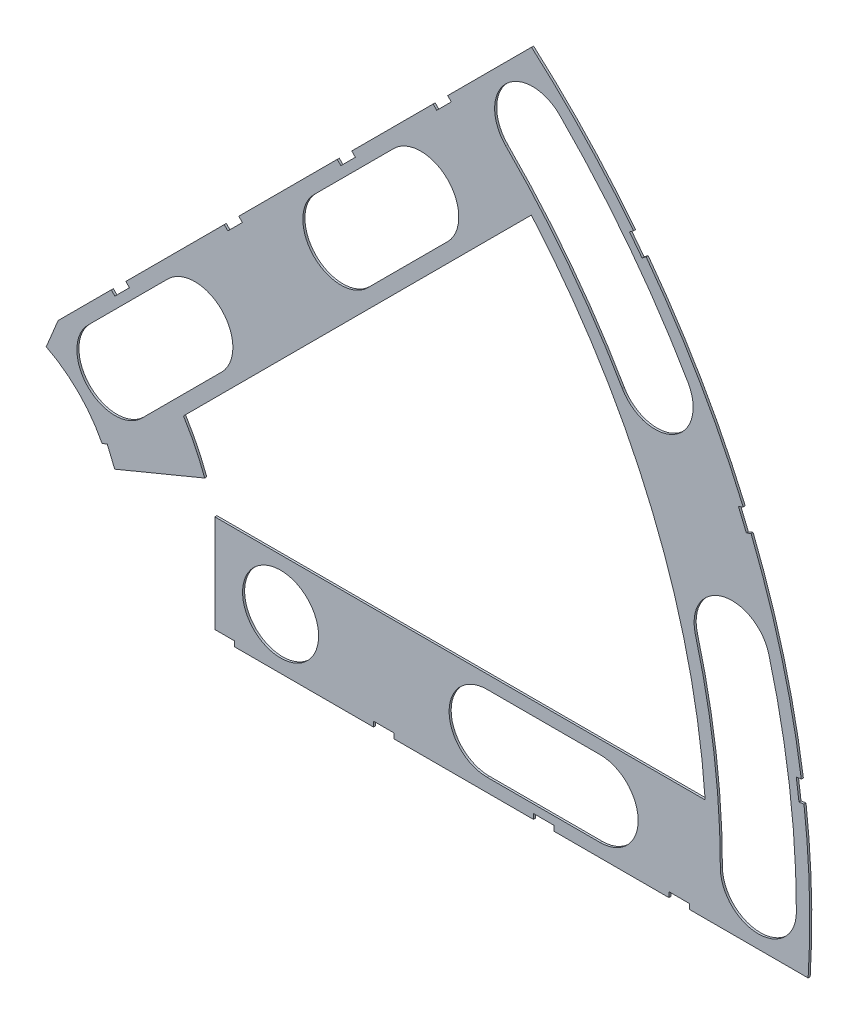
SolidWorks part; units mm, degrees
material "PTFE (general)"
ref_plane "Front Plane" through (0, 0, 0) normal (0, 0, 1) x (1, 0, 0)
ref_plane "Top Plane" through (0, 0, 0) normal (0, 1, 0) x (1, 0, 0)
ref_plane "Right Plane" through (0, 0, 0) normal (1, 0, 0) x (0, 0, -1)
sketch "Sketch1" plane through (0, 0, 0) normal (0, 0, 1) x (1, 0, 0)
  line L0 (0, 0) -> (320.3893, 0) construction
  line L1 (0, 0) -> (155.5285, 155.5285) construction
  line L2 (67.2115, 76.1917) -> (8.6967, 17.6769)
  line L3 (8.6967, 17.6769) -> (7.229, 14.1336)
  line L4 (101.4014, -6.35) -> (18.6489, -6.35)
  line L5 (15.1056, -4.8823) -> (18.6489, -6.35)
  line L6 (88.6729, 6.35) -> (27.8605, 6.35)
  line L9 (67.1914, 58.2111) -> (24.1905, 15.2102)
  line L10 (0, 0) -> (40.4486, 97.6516) construction
  line L11 (0, 0) -> (123.4567, -51.1374) construction
  line L18 (8.6967, 17.6769) -> (13.294, 8.6183) construction
  line L19 (18.6489, -6.35) -> (15.4943, 3.3063) construction
  line L20 (27.8605, 6.35) -> (27.7442, 6.7059) construction
  line L21 (24.1905, 15.2102) -> (24.3599, 14.8764) construction
  arc A0 (7.229, 14.1336) -> (15.1056, -4.8823) centre (0, 0) cw
  arc A1 (67.2115, 76.1917) -> (101.4014, -6.35) centre (0, 0) cw
  arc A2 (24.1905, 15.2102) -> (27.8605, 6.35) centre (0, 0) cw
  arc A3 (67.1914, 58.2111) -> (88.6729, 6.35) centre (0, 0) cw
  arc A8 (13.294, 8.6183) -> (15.4943, 3.3063) centre (0, 0) cw construction
  arc A9 (24.3599, 14.8764) -> (27.7442, 6.7059) centre (0, 0) cw construction
  dimension "D1" = 45
  dimension "D3" = 6.35
  dimension "D4" = 15.875
  dimension "D7" = 22.5
  dimension "D8" = 101.6
  dimension "D11" = 12.7
  dimension "D12" = 12.7
  dimension "D2" = 6.35
  dimension "D5" = 67.5
  dimension "D9" = 1.27
  dimension "D10" = 1.27
  dimension "D6" = 12.7
extrude "Boss-Extrude1" add sketch "Sketch1" along normal blind 0.254
sketch "Sketch2" plane through (0, 0, 0.254) normal (0, 0, 1) x (1, 0, 0)
  line L0 (0, 0) -> (101.6, 0) construction
  line L1 (0, 0) -> (71.842, 71.842) construction
  line L3 (0, 0) -> (22.225, 0) construction
  line L4 (0, 0) -> (15.7154, 15.7154) construction
  line L5 (0, 0) -> (95.25, 0) construction
  line L6 (0, 0) -> (92.0044, 24.6525) construction
  arc A0 (101.4014, -6.35) -> (67.2115, 76.1917) centre (0, 0) ccw construction
  circle A1 centre (22.225, 0) radius 4.699
  arc A2 (15.1056, -4.8823) -> (7.229, 14.1336) centre (0, 0) ccw construction
  circle A3 centre (36.195, 0) radius 4.699
  circle A4 centre (61.722, 0) radius 4.699
  circle A5 centre (75.692, 0) radius 4.699
  circle A6 centre (95.25, 0) radius 4.699
  circle A7 centre (15.7154, 15.7154) radius 4.699
  circle A8 centre (25.5937, 25.5937) radius 4.699
  circle A9 centre (43.644, 43.644) radius 4.699
  circle A10 centre (53.5223, 53.5223) radius 4.699
  circle A11 centre (92.0044, 24.6525) radius 4.699
  circle A12 centre (82.4889, 47.625) radius 4.699
  circle A13 centre (67.3519, 67.3519) radius 4.699
  dimension "D3" = 9.398
  dimension "D1" = 45
  dimension "D2" = 6.35
  dimension "D4" = 6.35
  dimension "D5" = 13.97
  dimension "D7" = 13.97
  dimension "D8" = 19.558
  dimension "D9" = 45
  dimension "D10" = 15
  dimension "D11" = 25.527
  dimension "D6" = 2
extrude "Cut-Extrude1" cut sketch "Sketch2" against normal through all
sketch "Sketch3" plane through (0, 0, 0.254) normal (0, 0, 1) x (1, 0, 0)
  line L0 (15.2664, 24.2467) -> (17.0625, 26.0427)
  line L1 (15.2664, 24.2467) -> (15.7154, 23.7977)
  line L2 (17.0625, 26.0427) -> (17.5115, 25.5937)
  line L3 (15.7154, 23.7977) -> (17.5115, 25.5937)
  line L4 (67.2115, 76.1917) -> (8.6967, 17.6769) construction
  line L5 (44.9911, 53.9713) -> (43.195, 52.1753)
  line L6 (44.9911, 53.9713) -> (45.4401, 53.5223)
  line L7 (43.195, 52.1753) -> (43.644, 51.7263)
  line L8 (45.4401, 53.5223) -> (43.644, 51.7263)
  line L9 (27.94, -6.35) -> (30.48, -6.35)
  line L10 (27.94, -6.35) -> (27.94, -5.715)
  line L11 (30.48, -6.35) -> (30.48, -5.715)
  line L12 (27.94, -5.715) -> (30.48, -5.715)
  line L13 (18.6489, -6.35) -> (101.4014, -6.35) construction
  line L14 (67.437, -6.35) -> (69.977, -6.35)
  line L15 (67.437, -6.35) -> (67.437, -5.715)
  line L16 (69.977, -6.35) -> (69.977, -5.715)
  line L17 (67.437, -5.715) -> (69.977, -5.715)
  line L18 (29.2307, 38.211) -> (31.0268, 40.007)
  line L19 (29.2307, 38.211) -> (29.6797, 37.762)
  line L20 (31.0268, 40.007) -> (31.4758, 39.558)
  line L21 (29.6797, 37.762) -> (31.4758, 39.558)
  line L22 (56.845, 65.8253) -> (55.049, 64.0292)
  line L23 (56.845, 65.8253) -> (57.294, 65.3763)
  line L24 (55.049, 64.0292) -> (55.498, 63.5802)
  line L25 (57.294, 65.3763) -> (55.498, 63.5802)
  line L26 (47.6885, -6.35) -> (50.2285, -6.35)
  line L27 (47.6885, -6.35) -> (47.6885, -5.715)
  line L28 (50.2285, -6.35) -> (50.2285, -5.715)
  line L29 (47.6885, -5.715) -> (50.2285, -5.715)
  line L30 (84.201, -6.35) -> (86.741, -6.35)
  line L31 (84.201, -6.35) -> (84.201, -5.715)
  line L32 (86.741, -6.35) -> (86.741, -5.715)
  line L33 (84.201, -5.715) -> (86.741, -5.715)
  line L34 (0, 0) -> (100.7308, 13.2615) construction
  line L35 (0, 0) -> (93.8662, 38.8806) construction
  line L36 (0, 0) -> (80.6047, 61.8502) construction
  line L37 (0, 0) -> (101.6, 0) construction
  line L38 (99.9355, 14.4377) -> (100.267, 11.9194)
  line L39 (99.9355, 14.4377) -> (101.1946, 14.6035)
  line L40 (100.267, 11.9194) -> (101.5261, 12.0852)
  line L41 (101.1946, 14.6035) -> (101.5261, 12.0852)
  line L42 (99.9355, 14.4377) -> (101.5261, 12.0852) construction
  line L43 (100.267, 11.9194) -> (101.1946, 14.6035) construction
  line L44 (93.7655, 37.4643) -> (94.9388, 37.9503)
  line L45 (93.7655, 37.4643) -> (92.7935, 39.811)
  line L46 (94.9388, 37.9503) -> (93.9668, 40.297)
  line L47 (92.7935, 39.811) -> (93.9668, 40.297)
  line L48 (93.7655, 37.4643) -> (93.9668, 40.297) construction
  line L49 (94.9388, 37.9503) -> (92.7935, 39.811) construction
  line L50 (79.3278, 62.4712) -> (80.874, 60.456)
  line L51 (79.3278, 62.4712) -> (80.3354, 63.2443)
  line L52 (80.874, 60.456) -> (81.8816, 61.2292)
  line L53 (80.3354, 63.2443) -> (81.8816, 61.2292)
  line L54 (79.3278, 62.4712) -> (81.8816, 61.2292) construction
  line L55 (80.874, 60.456) -> (80.3354, 63.2443) construction
  line L56 (13.5939, 7.0054) -> (14.5659, 4.6588)
  line L57 (13.5939, 7.0054) -> (14.7672, 7.4914)
  line L58 (14.5659, 4.6588) -> (15.7393, 5.1448)
  line L59 (14.7672, 7.4914) -> (15.7393, 5.1448)
  line L60 (13.5939, 7.0054) -> (15.7393, 5.1448) construction
  line L61 (14.5659, 4.6588) -> (14.7672, 7.4914) construction
  circle A0 centre (15.7154, 15.7154) radius 4.699 construction
  circle A1 centre (43.644, 43.644) radius 4.699 construction
  circle A2 centre (22.225, 0) radius 4.699 construction
  circle A3 centre (61.722, 0) radius 4.699 construction
  arc A4 (101.4014, -6.35) -> (67.2115, 76.1917) centre (0, 0) ccw construction
  arc A9 (15.1056, -4.8823) -> (7.229, 14.1336) centre (0, 0) ccw construction
  circle A10 centre (36.195, 0) radius 4.699 construction
  circle A11 centre (75.692, 0) radius 4.699 construction
  circle A12 centre (53.5223, 53.5223) radius 4.699 construction
  circle A13 centre (25.5937, 25.5937) radius 4.699 construction
  point P75 (14.6666, 6.0751)
  dimension "D2" = 5.715
  dimension "D3" = 2.54
  dimension "D6" = 5.715
  dimension "D8" = 0.635
  dimension "D9" = 5.715
  dimension "D12" = 5.715
  dimension "D4" = 7.5
  dimension "D5" = 22.5
  dimension "D7" = 37.5
  dimension "D10" = 90
  dimension "D11" = 1.27
  dimension "D14" = 0.635
  dimension "D15" = 90
  dimension "D18" = 0.635
  dimension "D19" = 90
  dimension "D22" = 0.635
  dimension "D20" = 1.27
  dimension "D17" = 0.635
  dimension "D13" = 11.4935
  dimension "D16" = 8.509
  dimension "D21" = 8.509
  dimension "D23" = 11.4935
extrude "Cut-Extrude2" cut sketch "Sketch3" against normal through all
sketch "Sketch5" plane through (0, 0, 0.254) normal (0, 0, 1) x (1, 0, 0)
  line L0 (11.6404, 3.5844) -> (28.067, 10.3886)
  line L1 (28.067, 10.3886) -> (28.067, -7.62)
  line L2 (28.067, -7.62) -> (11.6404, -7.62)
  line L3 (14.7672, 7.4914) -> (14.1336, 7.229) construction
  line L4 (11.6404, -7.62) -> (11.6404, 3.5844)
  line L5 (18.6489, -6.35) -> (27.94, -6.35) construction
  line L8 (30.48, -6.35) -> (30.48, -5.715) construction
  dimension "D1" = 2.413
  dimension "D2" = 1.27
  dimension "D3" = 2.413
  dimension "D4" = 17.78
sketch "Sketch6" plane through (0, 0, 0.254) normal (0, 0, 1) x (1, 0, 0)
  line L0 (0, 0) -> (101.6, 0) construction
  line L1 (0, 0) -> (71.842, 71.842) construction
  line L2 (0, 0) -> (87.9882, 50.8) construction
  line L3 (0, 0) -> (98.1381, 26.296) construction
  line L4 (15.7154, 15.7154) -> (25.5937, 25.5937) construction
  line L5 (12.3928, 19.0381) -> (22.271, 28.9164)
  line L6 (19.0381, 12.3928) -> (28.9164, 22.271)
  line L7 (43.644, 43.644) -> (53.5223, 53.5223) construction
  line L8 (40.3213, 46.9667) -> (50.1996, 56.845)
  line L9 (46.9667, 40.3213) -> (56.845, 50.1996)
  line L13 (61.722, 0) -> (75.692, 0) construction
  line L14 (61.722, 4.699) -> (75.692, 4.699)
  line L15 (61.722, -4.699) -> (75.692, -4.699)
  arc A0 (79.8253, 62.8529) -> (67.2115, 76.1917) centre (0, 0) ccw construction
  arc A1 (12.3928, 19.0381) -> (19.0381, 12.3928) centre (15.7154, 15.7154) ccw
  arc A2 (28.9164, 22.271) -> (22.271, 28.9164) centre (25.5937, 25.5937) ccw
  arc A3 (40.3213, 46.9667) -> (46.9667, 40.3213) centre (43.644, 43.644) ccw
  arc A4 (56.845, 50.1996) -> (50.1996, 56.845) centre (53.5223, 53.5223) ccw
  arc A5 (101.4014, -6.35) -> (100.8887, 12.0013) centre (0, 0) ccw construction
  circle A6 centre (53.5223, 53.5223) radius 4.699 construction
  arc A7 (93.3728, 40.0509) -> (81.3715, 60.8378) centre (0, 0) ccw construction
  arc A8 (100.5572, 14.5196) -> (94.3448, 37.7043) centre (0, 0) ccw construction
  circle A9 centre (25.5937, 25.5937) radius 4.699 construction
  arc A10 (61.722, 4.699) -> (61.722, -4.699) centre (61.722, 0) ccw
  arc A11 (75.692, -4.699) -> (75.692, 4.699) centre (75.692, 0) ccw
  arc A12 (95.25, 0) -> (92.0044, 24.6525) centre (0, 0) ccw construction
  arc A13 (99.949, 0) -> (96.5433, 25.8687) centre (0, 0) ccw
  arc A14 (90.551, 0) -> (87.4655, 23.4363) centre (0, 0) ccw
  arc A15 (90.551, 0) -> (99.949, 0) centre (95.25, 0) ccw
  arc A16 (96.5433, 25.8687) -> (87.4655, 23.4363) centre (92.0044, 24.6525) ccw
  arc A17 (82.4889, 47.625) -> (67.3519, 67.3519) centre (0, 0) ccw construction
  arc A18 (86.5584, 49.9745) -> (70.6746, 70.6746) centre (0, 0) ccw
  arc A19 (78.4195, 45.2755) -> (64.0292, 64.0292) centre (0, 0) ccw
  arc A20 (78.4195, 45.2755) -> (86.5584, 49.9745) centre (82.4889, 47.625) ccw
  arc A21 (70.6746, 70.6746) -> (64.0292, 64.0292) centre (67.3519, 67.3519) ccw
  point P4 (20.6546, 20.6546)
  point P13 (48.5832, 48.5832)
  point P48 (68.707, 0)
  point P61 (94.4351, 12.4326)
  point P68 (75.5669, 57.9845)
  dimension "D2" = 9.398
  dimension "D3" = 9.398
  dimension "D1" = 45
  dimension "D4" = 9.398
  dimension "D5" = 9.398
extrude "Cut-Extrude4" cut sketch "Sketch6" against normal through all
extrude "Cut-Extrude5" cut sketch "Sketch5" against normal through all
equation "\"cSep\"= 1.005"
equation "\"D11@Sketch2\"=\"cSep\""
equation "\"cSep2\"= \"D8@Sketch2\""
equation "\"D13@Sketch3\"=\"cSep\"/2-.05"
equation "\"D16@Sketch3\"=\"cSep2\"/2-.05"
equation "\"D21@Sketch3\"=\"cSep2\"/2-.05"
equation "\"D23@Sketch3\"=\"cSep\"/2-.05"
